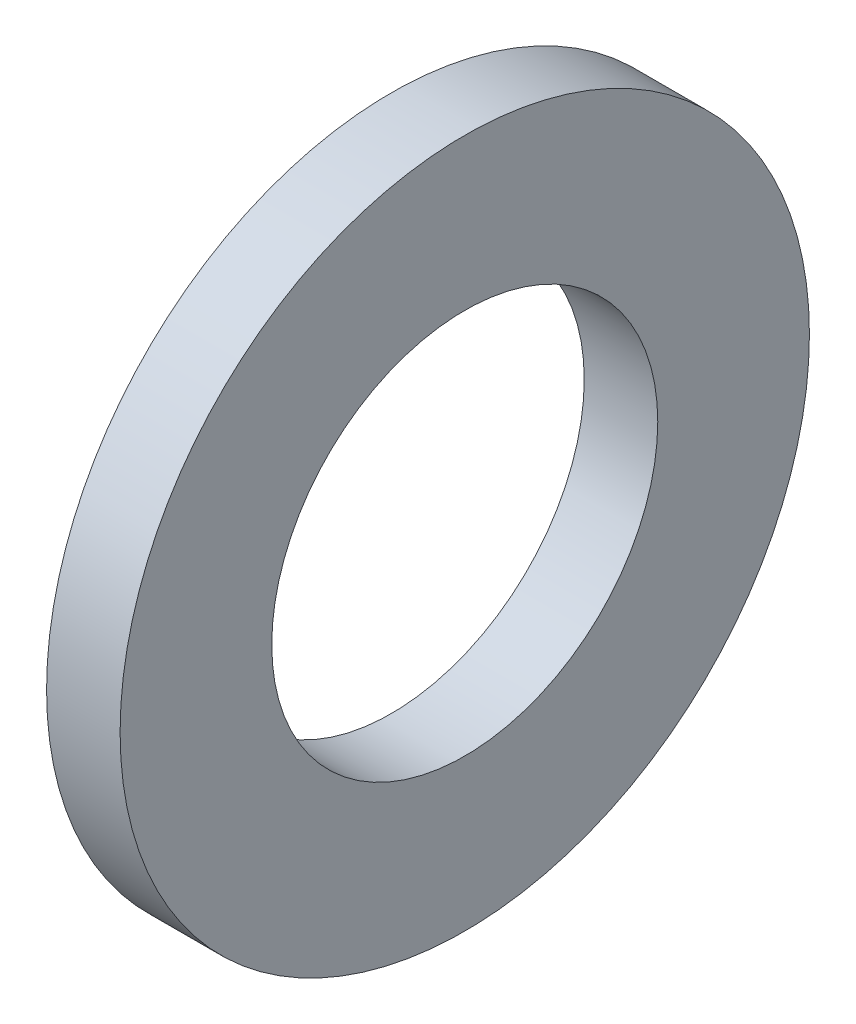
SolidWorks part; units mm, degrees
ref_plane "Plane1" through (0, 0, 0) normal (0, 0, 1) x (1, 0, 0)
ref_plane "Plane2" through (0, 0, 0) normal (0, 1, 0) x (1, 0, 0)
ref_plane "Plane3" through (0, 0, 0) normal (1, 0, 0) x (0, 0, -1)
sketch "Sketch1" plane through (0, 0, 0) normal (0, 0, 1) x (1, 0, 0)
  line L0 (-34.925, 0) -> (9.525, 0) construction
  line L1 (0, 4.2) -> (0, 7.5)
  line L2 (0, 7.5) -> (-1.6, 7.5)
  line L3 (-1.6, 7.5) -> (-1.6, 4.2)
  line L4 (-1.6, 4.2) -> (0, 4.2)
  dimension "Thickness" = 1.6
  dimension "Inside_dia" = 8.4
  dimension "Outside_dia" = 15
revolve "Base-Revolve" add sketch "Sketch1" angle 360 about L0
